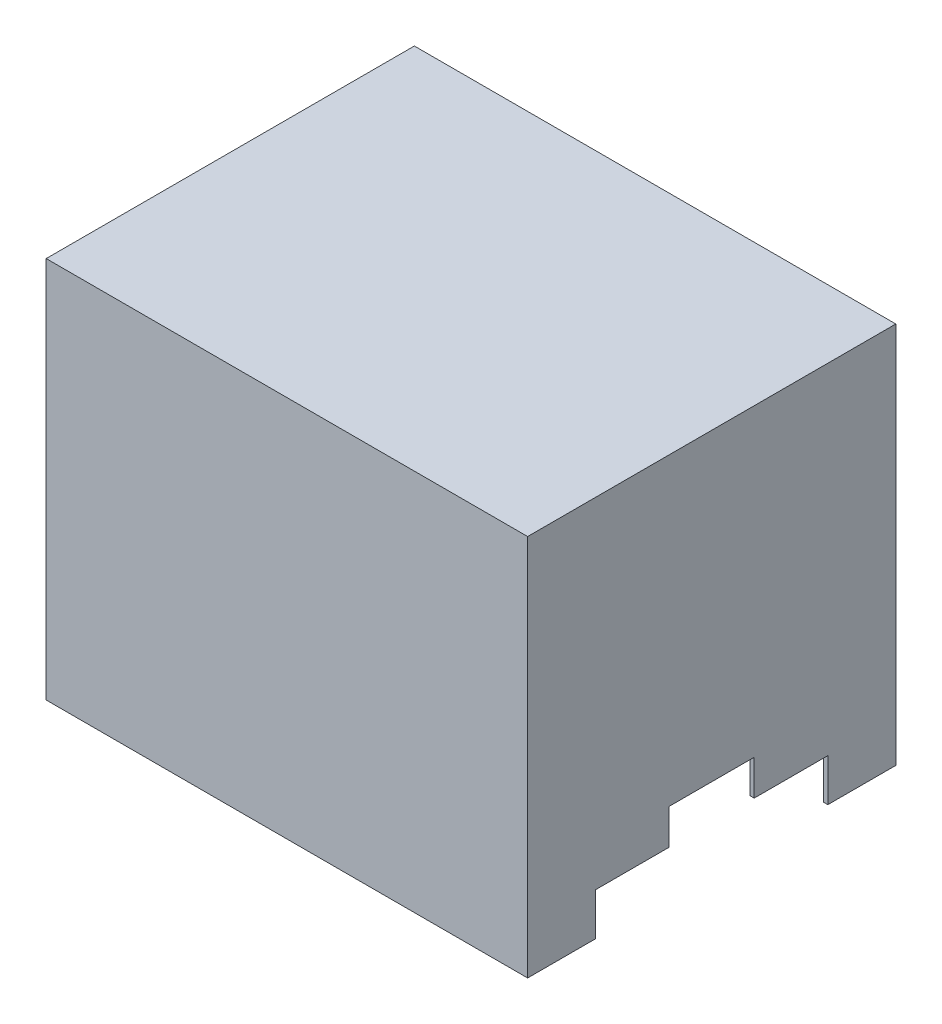
SolidWorks part; units mm, degrees
ref_plane "Alzado" through (0, 0, 0) normal (0, 0, 1) x (1, 0, 0)
ref_plane "Planta" through (0, 0, 0) normal (0, 1, 0) x (1, 0, 0)
ref_plane "Vista lateral" through (0, 0, 0) normal (1, 0, 0) x (0, 0, -1)
sketch "Croquis1" plane through (0, 0, 0) normal (0, 1, 0) x (1, 0, 0)
  line L1 (-170, 130) -> (170, 130)
  line L2 (-170, 130) -> (-170, -130)
  line L3 (-170, -130) -> (170, -130)
  line L4 (170, 130) -> (170, -130)
  line L5 (-170, 130) -> (170, -130) construction
  line L6 (-170, -130) -> (170, 130) construction
  point P0 (0, 0)
  dimension "D1" = 340
  dimension "D2" = 260
extrude "Saliente-Extruir1" add sketch "Croquis1" along normal blind 270
sketch "Croquis2" plane through (0, 0, 0) normal (0, -1, 0) x (1, 0, 0)
  line L0 (-170, -130) -> (-170, 130) construction
  line L1 (-167, 127) -> (167, 127)
  line L2 (-167, 127) -> (-167, -127)
  line L3 (-167, -127) -> (167, -127)
  line L4 (167, 127) -> (167, -127)
  line L5 (-167, 127) -> (167, -127) construction
  line L6 (-167, -127) -> (167, 127) construction
  line L7 (-170, 130) -> (170, 130) construction
  point P0 (0, 0)
  dimension "D1" = 3
  dimension "D2" = 3
extrude "Cortar-Extruir1" cut sketch "Croquis2" against normal blind 267
sketch "Croquis3" plane through (170, 0, 0) normal (1, 0, 0) x (0, 0, -1)
  line L0 (0, 0) -> (-82, 0)
  line L1 (-130, 0) -> (130, 0) construction
  line L2 (-82, 0) -> (-82, 30)
  line L3 (-82, 30) -> (-30, 30)
  line L4 (-30, 30) -> (-30, 55)
  line L5 (-30, 55) -> (30, 55)
  line L6 (30, 55) -> (30, 30)
  line L7 (30, 30) -> (82, 30)
  line L8 (82, 30) -> (82, 0)
  line L9 (82, 0) -> (0, 0)
  line L10 (-130, 270) -> (130, 270) construction
  point P14 (0, 55)
  dimension "D1" = 164
  dimension "D2" = 82
  dimension "D3" = 240
  dimension "D4" = 240
  dimension "D5" = 60
  dimension "D6" = 0
  dimension "D7" = 25
extrude "Cortar-Extruir2" cut sketch "Croquis3" against normal through all
